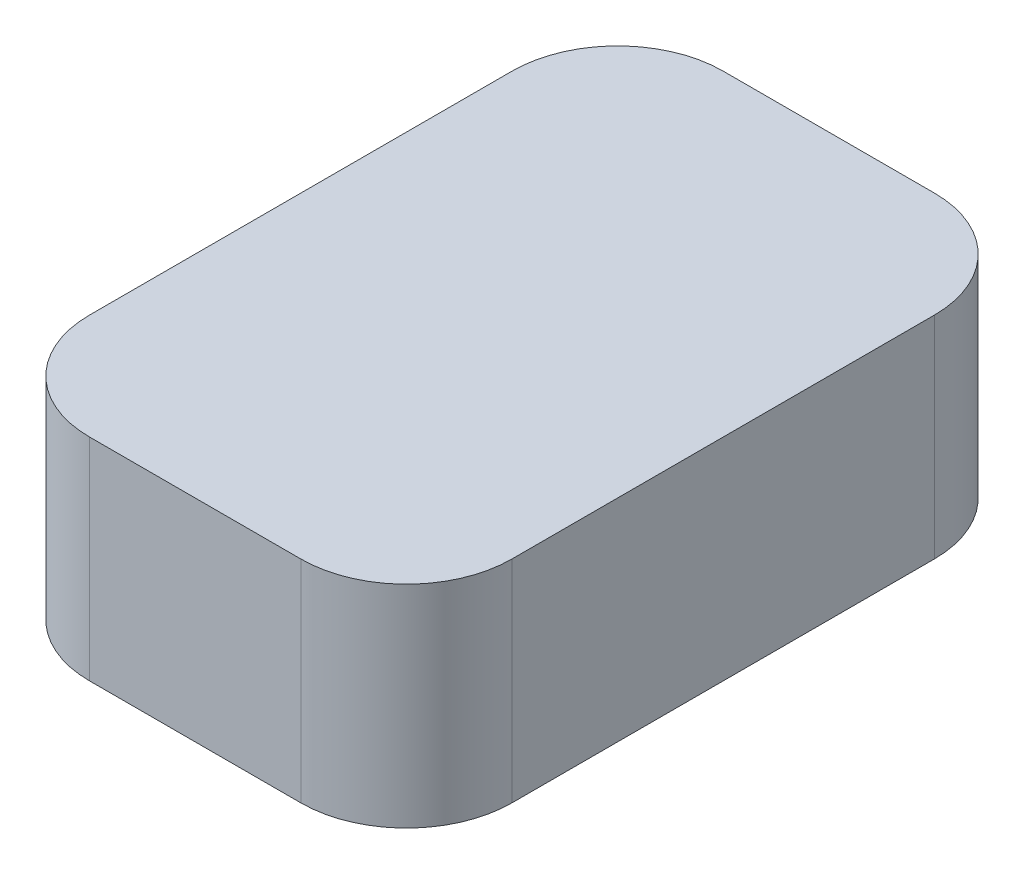
SolidWorks part; units mm, degrees
material "1023 Carbon Steel Sheet (SS)"
ref_plane "Front Plane" through (0, 0, 0) normal (0, 0, 1) x (1, 0, 0)
ref_plane "Top Plane" through (0, 0, 0) normal (0, 1, 0) x (1, 0, 0)
ref_plane "Right Plane" through (0, 0, 0) normal (1, 0, 0) x (0, 0, -1)
sketch "Sketch2" plane through (0, 0, 0) normal (0, 1, 0) x (1, 0, 0)
  line L1 (-10, -15) -> (10, -15)
  line L2 (-10, -15) -> (-10, 15)
  line L3 (-10, 15) -> (10, 15)
  line L4 (10, -15) -> (10, 15)
  line L5 (-10, -15) -> (10, 15) construction
  line L6 (-10, 15) -> (10, -15) construction
  point P0 (0, 0)
  dimension "D1" = 30
  dimension "D2" = 20
extrude "Boss-Extrude1" add sketch "Sketch2" against normal blind 10
fillet "Fillet1" radius 5 4 edges at (10, -5, -15) (-10, -5, -15) (-10, -5, 15) (10, -5, 15)
